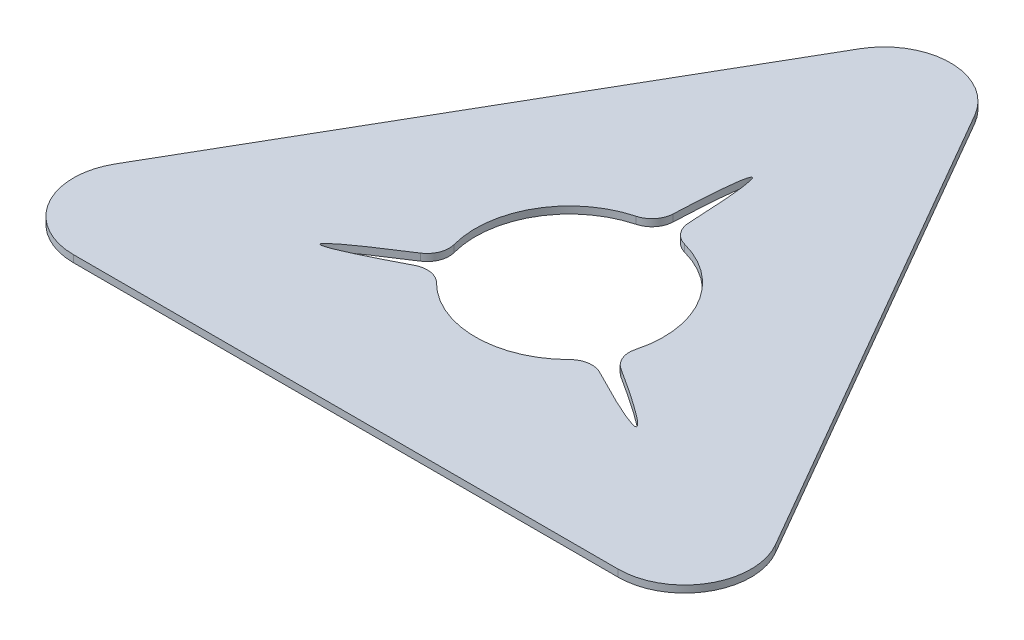
SolidWorks part; units mm, degrees
material "Beech"
ref_plane "Front Plane" through (0, 0, 0) normal (0, 0, 1) x (1, 0, 0)
ref_plane "Top Plane" through (0, 0, 0) normal (0, 1, 0) x (1, 0, 0)
ref_plane "Right Plane" through (0, 0, 0) normal (1, 0, 0) x (0, 0, -1)
sketch "Sketch1" plane through (0, 0, 0) normal (0, 1, 0) x (1, 0, 0)
  line L0 (0, 0) -> (-350, -606.2178)
  line L1 (-350, -606.2178) -> (350, -606.2178)
  line L2 (350, -606.2178) -> (0, 0)
extrude "Boss-Extrude1" add sketch "Sketch1" along normal blind 6.35
sketch "Sketch2" plane through (0, 6.35, 0) normal (0, 1, 0) x (1, 0, 0)
  circle A0 centre (0, -404.1452) radius 85
  dimension "D1" = 170
extrude "Cut-Extrude1" cut sketch "Sketch2" against normal blind 6.35
fillet "Fillet1" radius 60 3 edges at (0, 3.175, 0) (350, 3.175, 606.2178) (-350, 3.175, 606.2178)
sketch "Sketch3" plane through (0, 6.35, 0) normal (0, 1, 0) x (1, 0, 0)
  line L0 (30.4808, -411.351) -> (21.4808, -426.9394)
  line L1 (-9, -374.1452) -> (9, -374.1452)
  line L2 (-21.4808, -426.9394) -> (-30.4808, -411.351)
  circle A0 centre (0, -404.1452) radius 85 construction
  conic Q0 (-9, -374.1452) -> (9, -374.1452) control (0, 225.8548) rho 0.225
  conic Q1 (30.4808, -411.351) -> (21.4808, -426.9394) control (545.596, -719.1452) rho 0.225
  conic Q2 (-21.4808, -426.9394) -> (-30.4808, -411.351) control (-545.596, -719.1452) rho 0.225
  point P4 (0, -374.1452)
  point P18 (0, -404.1452)
  point P19 (0, -404.1452)
  dimension "D1" = 0
  dimension "D2" = 30
  dimension "D3" = 18
  dimension "D4" = 600
  dimension "D5" = 135
  dimension "D6" = 3
extrude "Cut-Extrude2" cut sketch "Sketch3" against normal blind 6.35
fillet "Fillet2" radius 20 6 edges at (-7.6774, 3.175, 319.4926) (7.6774, 3.175, 319.4926) (77.15, 3.175, 439.8226) (69.4726, 3.175, 453.1203) (-69.4726, 3.175, 453.1203) (-77.15, 3.175, 439.8226)
